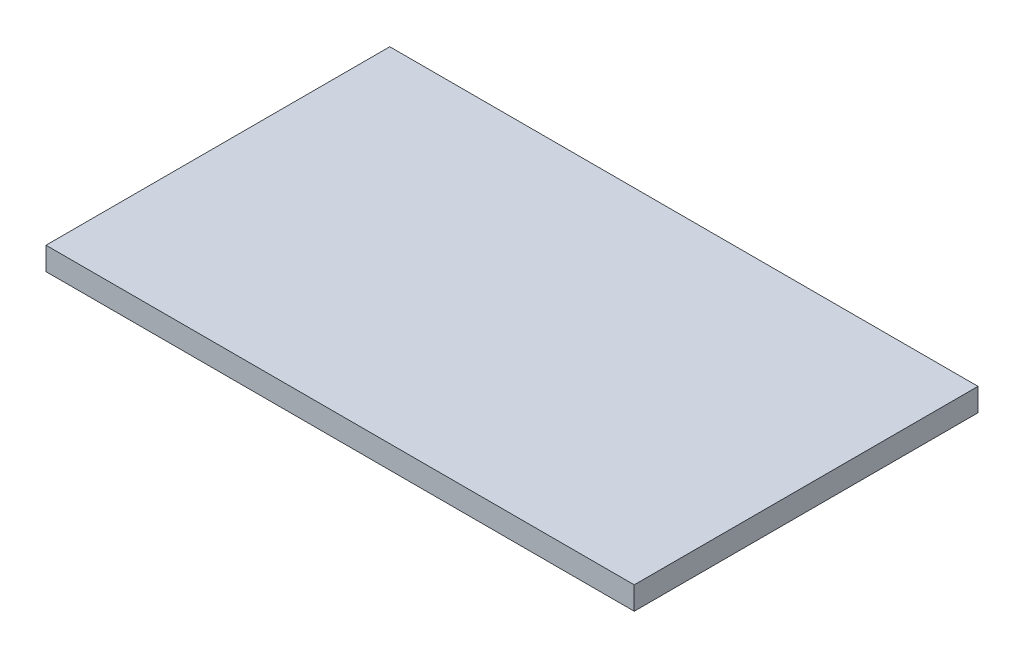
SolidWorks part; units mm, degrees
ref_plane "Front Plane" through (0, 0, 0) normal (0, 0, 1) x (1, 0, 0)
ref_plane "Top Plane" through (0, 0, 0) normal (0, 1, 0) x (1, 0, 0)
ref_plane "Right Plane" through (0, 0, 0) normal (1, 0, 0) x (0, 0, -1)
sketch "Sketch1" plane through (0, 0, 0) normal (0, 1, 0) x (1, 0, 0)
  line L1 (-36.5928, 17.5704) -> (40.4072, 17.5704)
  line L2 (-36.5928, 17.5704) -> (-36.5928, -27.4296)
  line L3 (-36.5928, -27.4296) -> (40.4072, -27.4296)
  line L4 (40.4072, 17.5704) -> (40.4072, -27.4296)
  dimension "D1" = 77
  dimension "D2" = 45
extrude "Boss-Extrude1" add sketch "Sketch1" along normal blind 3
